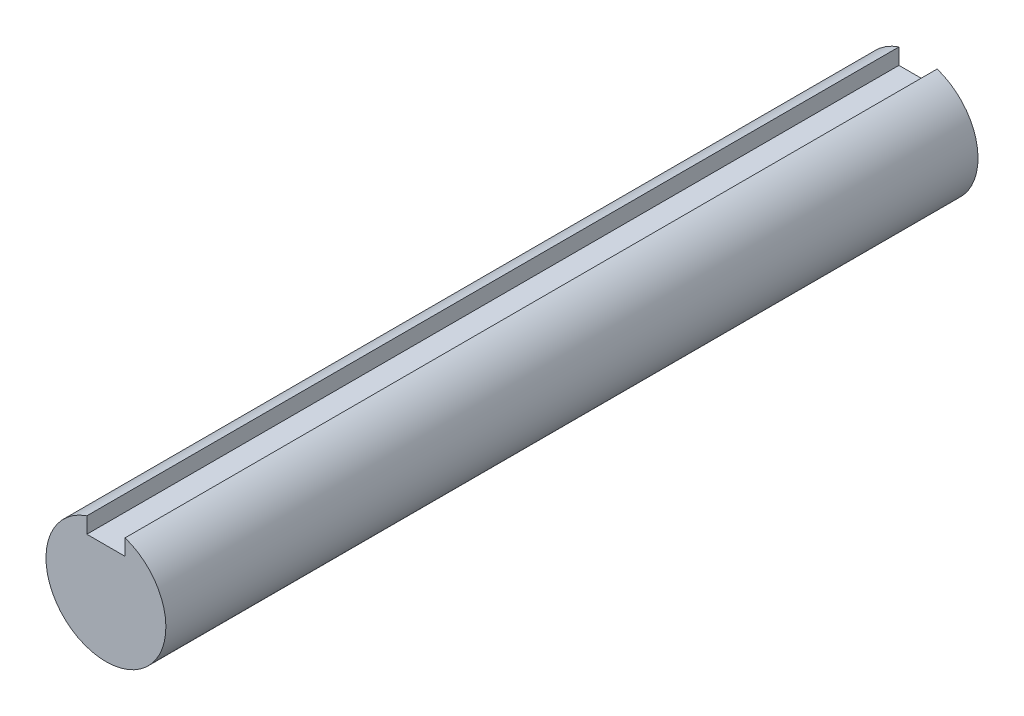
SolidWorks part; units mm, degrees
ref_plane "Front Plane" through (0, 0, 0) normal (0, 0, 1) x (1, 0, 0)
ref_plane "Top Plane" through (0, 0, 0) normal (0, 1, 0) x (1, 0, 0)
ref_plane "Right Plane" through (0, 0, 0) normal (1, 0, 0) x (0, 0, -1)
sketch "Sketch1" plane through (0, 0, 0) normal (0, 0, 1) x (1, 0, 0)
  circle A0 centre (0, 0) radius 7.5
  dimension "D1" = 15
extrude "Boss-Extrude1" add sketch "Sketch1" along normal blind 101.6
sketch "Sketch2" plane through (0, 0, 101.6) normal (0, 0, 1) x (1, 0, 0)
  line L0 (0, 0) -> (0, 7.5) construction
  line L1 (-2.39, 7.5) -> (2.39, 7.5)
  line L2 (2.39, 7.5) -> (2.39, 5.11)
  line L3 (-2.39, 7.5) -> (-2.39, 5.11)
  line L4 (-2.39, 5.11) -> (2.39, 5.11)
  circle A0 centre (0, 0) radius 7.5 construction
  dimension "D1" = 2.39
  dimension "D2" = 2.39
extrude "Cut-Extrude1" cut sketch "Sketch2" against normal through all
